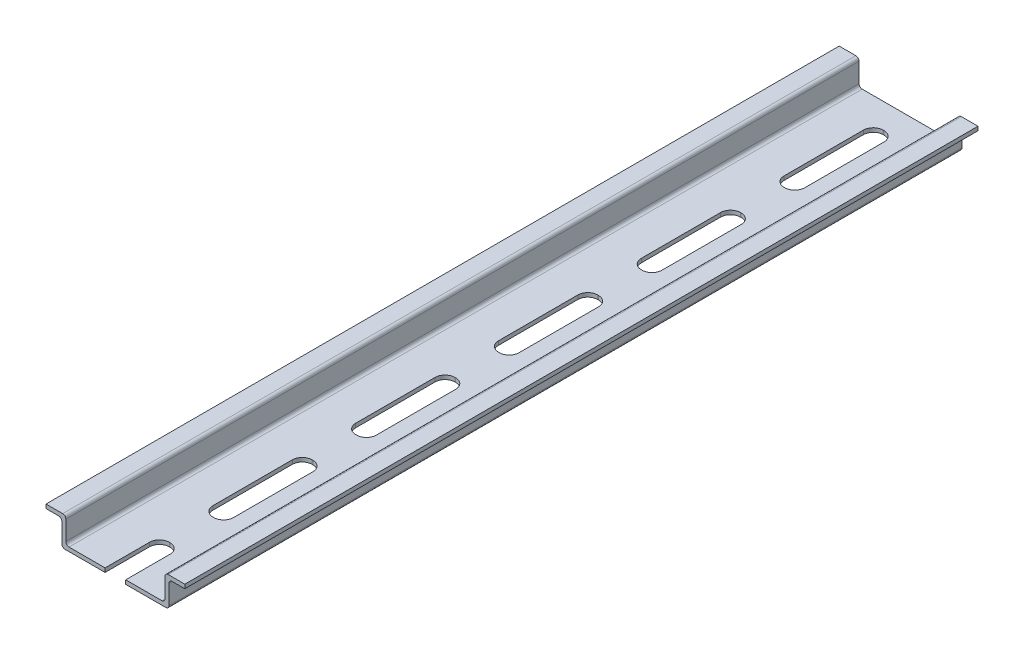
SolidWorks part; units mm, degrees
ref_plane "Front Plane" through (0, 0, 0) normal (0, 0, 1) x (1, 0, 0)
ref_plane "Top Plane" through (0, 0, 0) normal (0, 1, 0) x (1, 0, 0)
ref_plane "Right Plane" through (0, 0, 0) normal (1, 0, 0) x (0, 0, -1)
sketch "Sketch1" plane through (0, 0, 0) normal (0, 0, 1) x (1, 0, 0)
  line L0 (0, 0) -> (0, 1)
  line L1 (0, 1) -> (4.2, 1)
  line L2 (5, 0.2) -> (5, -4.7)
  line L3 (5.8, -5.5) -> (29.2, -5.5)
  line L4 (30, -4.7) -> (30, 0.2)
  line L5 (30.8, 1) -> (35, 1)
  line L6 (35, 1) -> (35, 0)
  line L7 (35, 0) -> (31.8, 0)
  line L8 (31, -0.8) -> (31, -5.7)
  line L9 (30.2, -6.5) -> (4.8, -6.5)
  line L10 (4, -5.7) -> (4, -0.8)
  line L11 (3.2, 0) -> (0, 0)
  arc A0 (4.8, -6.5) -> (4, -5.7) centre (4.8, -5.7) cw
  arc A1 (5, -4.7) -> (5.8, -5.5) centre (5.8, -4.7) ccw
  arc A2 (31, -5.7) -> (30.2, -6.5) centre (30.2, -5.7) cw
  arc A3 (29.2, -5.5) -> (30, -4.7) centre (29.2, -4.7) ccw
  arc A4 (31.8, 0) -> (31, -0.8) centre (31.8, -0.8) ccw
  arc A5 (30, 0.2) -> (30.8, 1) centre (30.8, 0.2) cw
  arc A6 (4.2, 1) -> (5, 0.2) centre (4.2, 0.2) cw
  arc A7 (4, -0.8) -> (3.2, 0) centre (3.2, -0.8) ccw
  dimension "D7" = 0.8
  dimension "D1" = 1
  dimension "D2" = 27
  dimension "D3" = 7.5
  dimension "D4" = 35
  dimension "D5" = 1
  dimension "D6" = 1
extrude "Boss-Extrude1" add sketch "Sketch1" along normal blind 200
sketch "Sketch2" plane through (0, -5.5, 0) normal (0, 1, 0) x (1, 0, 0)
  line L0 (29.2, 0) -> (5.8, 0) construction
  line L1 (17.4, -6.3009) -> (17.6, -6.3009)
  line L2 (14.9, -8.8009) -> (14.9, -28.8009)
  line L3 (17.4, -31.3009) -> (17.6, -31.3009)
  line L4 (20.1, -8.8009) -> (20.1, -28.8009)
  line L5 (14.9, -44.8009) -> (14.9, -64.8009)
  line L6 (17.4, -42.3009) -> (17.6, -42.3009)
  line L7 (20.1, -44.8009) -> (20.1, -64.8009)
  line L8 (17.4, -67.3009) -> (17.6, -67.3009)
  line L9 (14.9, -80.8009) -> (14.9, -100.8009)
  line L10 (17.4, -78.3009) -> (17.6, -78.3009)
  line L11 (20.1, -80.8009) -> (20.1, -100.8009)
  line L12 (17.4, -103.3009) -> (17.6, -103.3009)
  line L13 (14.9, -116.8009) -> (14.9, -136.8009)
  line L14 (17.4, -114.3009) -> (17.6, -114.3009)
  line L15 (20.1, -116.8009) -> (20.1, -136.8009)
  line L16 (17.4, -139.3009) -> (17.6, -139.3009)
  line L17 (14.9, -152.8009) -> (14.9, -172.8009)
  line L18 (17.4, -150.3009) -> (17.6, -150.3009)
  line L19 (20.1, -152.8009) -> (20.1, -172.8009)
  line L20 (17.4, -175.3009) -> (17.6, -175.3009)
  line L21 (14.9, -188.8009) -> (14.9, -208.8009)
  line L22 (17.4, -186.3009) -> (17.6, -186.3009)
  line L23 (20.1, -188.8009) -> (20.1, -208.8009)
  line L24 (17.4, -211.3009) -> (17.6, -211.3009)
  arc A0 (17.6, -31.3009) -> (20.1, -28.8009) centre (17.6, -28.8009) ccw
  arc A1 (14.9, -28.8009) -> (17.4, -31.3009) centre (17.4, -28.8009) ccw
  arc A2 (17.6, -6.3009) -> (20.1, -8.8009) centre (17.6, -8.8009) cw
  arc A3 (17.4, -6.3009) -> (14.9, -8.8009) centre (17.4, -8.8009) ccw
  arc A4 (17.4, -42.3009) -> (14.9, -44.8009) centre (17.4, -44.8009) ccw
  arc A5 (14.9, -64.8009) -> (17.4, -67.3009) centre (17.4, -64.8009) ccw
  arc A6 (17.6, -42.3009) -> (20.1, -44.8009) centre (17.6, -44.8009) cw
  arc A7 (17.6, -67.3009) -> (20.1, -64.8009) centre (17.6, -64.8009) ccw
  arc A8 (17.4, -78.3009) -> (14.9, -80.8009) centre (17.4, -80.8009) ccw
  arc A9 (14.9, -100.8009) -> (17.4, -103.3009) centre (17.4, -100.8009) ccw
  arc A10 (17.6, -78.3009) -> (20.1, -80.8009) centre (17.6, -80.8009) cw
  arc A11 (17.6, -103.3009) -> (20.1, -100.8009) centre (17.6, -100.8009) ccw
  arc A12 (17.4, -114.3009) -> (14.9, -116.8009) centre (17.4, -116.8009) ccw
  arc A13 (14.9, -136.8009) -> (17.4, -139.3009) centre (17.4, -136.8009) ccw
  arc A14 (17.6, -114.3009) -> (20.1, -116.8009) centre (17.6, -116.8009) cw
  arc A15 (17.6, -139.3009) -> (20.1, -136.8009) centre (17.6, -136.8009) ccw
  arc A16 (17.4, -150.3009) -> (14.9, -152.8009) centre (17.4, -152.8009) ccw
  arc A17 (14.9, -172.8009) -> (17.4, -175.3009) centre (17.4, -172.8009) ccw
  arc A18 (17.6, -150.3009) -> (20.1, -152.8009) centre (17.6, -152.8009) cw
  arc A19 (17.6, -175.3009) -> (20.1, -172.8009) centre (17.6, -172.8009) ccw
  arc A20 (17.4, -186.3009) -> (14.9, -188.8009) centre (17.4, -188.8009) ccw
  arc A21 (14.9, -208.8009) -> (17.4, -211.3009) centre (17.4, -208.8009) ccw
  arc A22 (17.6, -186.3009) -> (20.1, -188.8009) centre (17.6, -188.8009) cw
  arc A23 (17.6, -211.3009) -> (20.1, -208.8009) centre (17.6, -208.8009) ccw
  point P6 (17.5, 0)
  point P7 (17.5, -6.3009)
  point P12 (14.9, -31.3009)
  point P15 (20.1, -6.3009)
  point P18 (14.9, -6.3009)
  dimension "D3" = 2.5
  dimension "D1" = 5.2
  dimension "D2" = 25
  dimension "D4" = 6
extrude "Cut-Extrude1" cut sketch "Sketch2" against normal through all
